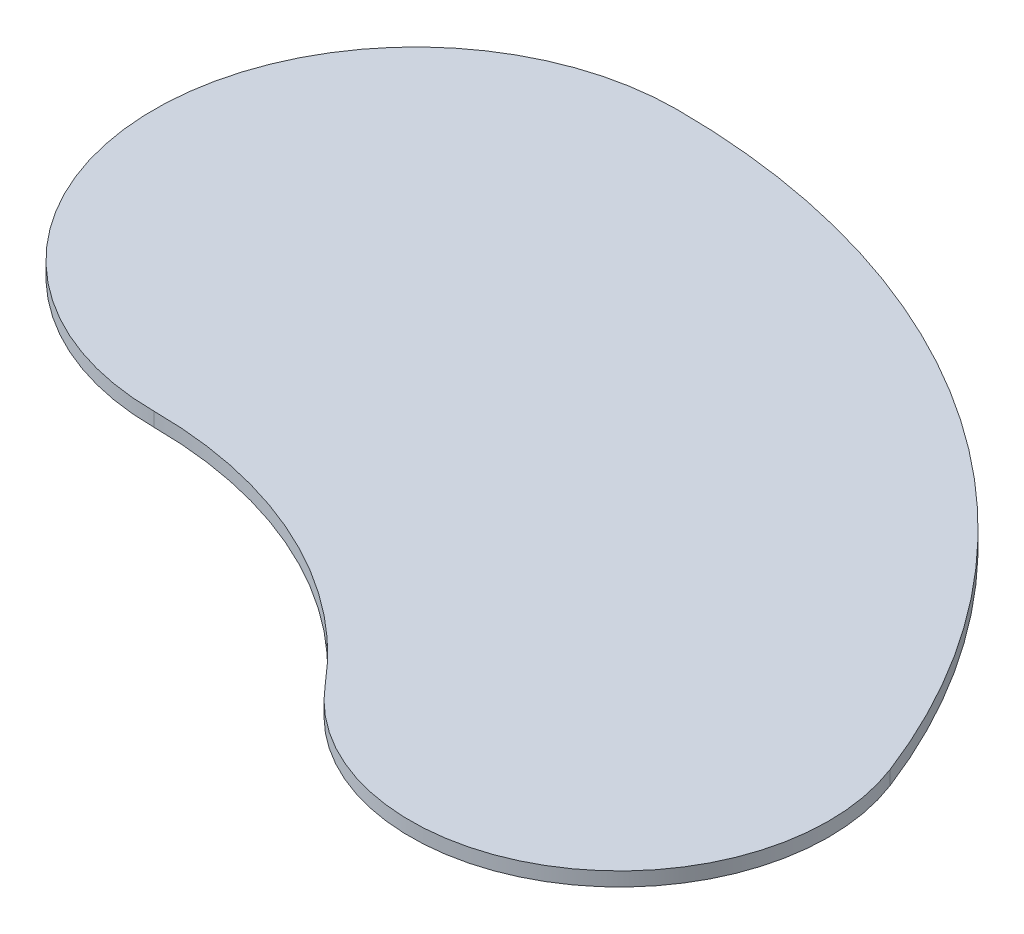
SolidWorks part; units mm, degrees
ref_plane "Front Plane" through (0, 0, 0) normal (0, 0, 1) x (1, 0, 0)
ref_plane "Top Plane" through (0, 0, 0) normal (0, 1, 0) x (1, 0, 0)
ref_plane "Right Plane" through (0, 0, 0) normal (1, 0, 0) x (0, 0, -1)
sketch "Sketch1" plane through (0, 0, 0) normal (0, 1, 0) x (1, 0, 0)
  line L0 (0, 232.3594) -> (0, 0) construction
  line L1 (0, 0) -> (87.9882, 50.8) construction
  circle A0 centre (0, 0) radius 101.6 construction
  arc A5 (0, 149.225) -> (0, 53.975) centre (0, 101.6) ccw
  arc A6 (58.6901, 26.4436) -> (123.5264, 64.5349) centre (87.9882, 50.8) ccw
  circle A9 centre (0, 0) radius 53.975 construction
  circle A10 centre (0, 0) radius 149.225 construction
  arc A11 (0, 53.975) -> (58.6901, 26.4436) centre (0, -22.3471) cw
  arc A12 (0, 149.225) -> (123.5264, 64.5349) centre (0, 16.7941) cw
  dimension "D1" = 47.625
  dimension "D2" = 38.1
  dimension "D4" = 203.2
  dimension "D3" = 60
extrude "Boss-Extrude1" add sketch "Sketch1" along normal blind 2.54 contours A5 A11 A6 A12
